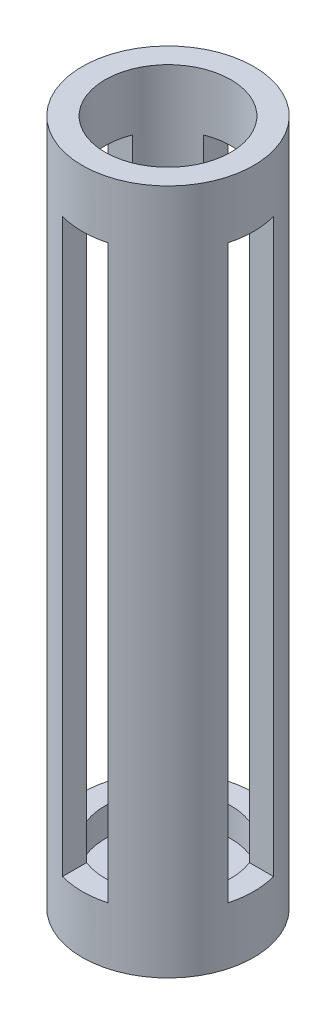
SolidWorks part; units mm, degrees
ref_plane "Front Plane" through (0, 0, 0) normal (0, 0, 1) x (1, 0, 0)
ref_plane "Top Plane" through (0, 0, 0) normal (0, 1, 0) x (1, 0, 0)
ref_plane "Right Plane" through (0, 0, 0) normal (1, 0, 0) x (0, 0, -1)
sketch "Sketch1" plane through (0, 0, 0) normal (0, 1, 0) x (1, 0, 0)
  circle A0 centre (0, 0) radius 13.97
  circle A1 centre (0, 0) radius 19.05
  dimension "D1" = 27.94
  dimension "D2" = 38.1
extrude "Boss-Extrude1" add sketch "Sketch1" along normal blind 152.4
sketch "Sketch2" plane through (0, 0, 0) normal (0, -1, 0) x (1, 0, 0)
  circle A0 centre (0, 0) radius 13.97
extrude "Boss-Extrude2" add sketch "Sketch2" against normal blind 6.35
ref_plane "Plane1" through (0, 0, 16.51) normal (0, 0, 1) x (1, 0, 0)
sketch "Sketch3" plane through (0, 0, 16.51) normal (0, 0, 1) x (1, 0, 0)
  line L0 (-19.05, 0) -> (19.05, 0) construction
  line L1 (0, 101.6) -> (0, 0) construction
  circle A0 centre (0, 101.6) radius 2.2479
  dimension "D1" = 4.4958
  dimension "D2" = 101.6
extrude "Cut-Extrude1" cut sketch "Sketch3" against normal through all and the other way through all contours A0
sketch "Sketch5" plane through (0, 0, 0) normal (1, 0, 0) x (0, 0, -1)
  line L0 (55, 0) -> (-55, 0) construction
  line L1 (5.08, 12.7) -> (-5.08, 12.7)
  line L2 (5.08, 12.7) -> (5.08, 139.7)
  line L3 (5.08, 139.7) -> (-5.08, 139.7)
  line L4 (-5.08, 12.7) -> (-5.08, 139.7)
  line L5 (19.05, 152.4) -> (-19.05, 152.4) construction
  line L6 (0, 0) -> (0, 12.7) construction
  line L7 (-5.08, 114.3) -> (7.62, 114.3)
  line L8 (-5.08, 88.9) -> (7.62, 88.9)
  line L9 (-5.08, 165.1) -> (5.08, 165.1)
  line L10 (-5.08, 190.5) -> (5.08, 190.5)
  dimension "D1" = 12.7
  dimension "D2" = 12.7
  dimension "D3" = 10.16
  dimension "D4" = 12.7
  dimension "D5" = 12.7
  dimension "D6" = 76.2
  dimension "D7" = 25.4
  dimension "D8" = 25.4
  dimension "D9" = 50.8
extrude "Cut-Extrude5" cut sketch "Sketch5" against normal through all both and the other way through all contours L8 L4 L1 L2 | L9 L4 L7 L2 | L4 L10 L2 L3
sketch "Sketch8" plane through (0, 0, 0) normal (0, 0, 1) x (1, 0, 0)
  line L0 (-19.05, 0) -> (19.05, 0) construction
  line L1 (5.08, 12.7) -> (-5.08, 12.7)
  line L2 (5.08, 12.7) -> (5.08, 139.7)
  line L3 (5.08, 139.7) -> (-5.08, 139.7)
  line L4 (-5.08, 12.7) -> (-5.08, 139.7)
  line L5 (19.05, 152.4) -> (-19.05, 152.4) construction
  line L6 (0, 12.7) -> (0, 0) construction
  line L7 (5.08, 88.9) -> (-5.08, 88.9)
  line L8 (5.08, 114.3) -> (-5.08, 114.3)
  line L9 (5.08, 165.1) -> (-5.08, 165.1)
  line L10 (5.08, 190.5) -> (-5.08, 190.5)
  dimension "D1" = 12.7
  dimension "D2" = 10.16
  dimension "D3" = 12.7
  dimension "D4" = 76.2
  dimension "D5" = 25.4
  dimension "D6" = 25.4
  dimension "D7" = 50.8
extrude "Cut-Extrude6" cut sketch "Sketch8" against normal through all both and the other way through all contours L2 L7 L4 L1 | L2 L9 L4 L8 | L10 L2 L3 L4
sketch "Sketch7" plane through (0, 6.35, 0) normal (0, 1, 0) x (1, 0, 0)
  circle A0 centre (0, 0) radius 6.35
extrude "Cut-Extrude4" cut sketch "Sketch7" against normal through all
ref_plane "Plane2" through (0, 45.72, 0) normal (0, -1, 0) x (-1, 0, 0)
sketch "Sketch9" plane through (0, 45.72, 0) normal (0, -1, 0) x (-1, 0, 0)
  line L2 (-11.7877, -7.4973) -> (-8.5729, -5.4526)
  line L7 (-6.0813, -12.5769) -> (-4.4227, -9.1469)
  line L8 (11.7877, 7.4973) -> (8.5729, 5.4526)
  line L9 (6.0813, 12.5769) -> (4.4227, 9.1469)
  circle A0 centre (0, 0) radius 13.97 construction
  arc A3 (-11.7877, -7.4973) -> (-6.0813, -12.5769) centre (0, 0) ccw
  arc A7 (-8.5729, -5.4526) -> (-4.4227, -9.1469) centre (0, 0) ccw
  arc A10 (8.5729, 5.4526) -> (4.4227, 9.1469) centre (0, 0) ccw
  circle A15 centre (0, 0) radius 13.97 construction
  circle A16 centre (0, 0) radius 10.16 construction
  arc A17 (11.7877, 7.4973) -> (6.0813, 12.5769) centre (0, 0) ccw
  point P16 (0, 0)
  dimension "D2" = 3.2148
  dimension "D3" = 3.4301
  dimension "D4" = 2
  dimension "D5" = 3.4301
  dimension "D1" = 3.81
extrude "Boss-Extrude3" add sketch "Sketch9" against normal blind 2.54
